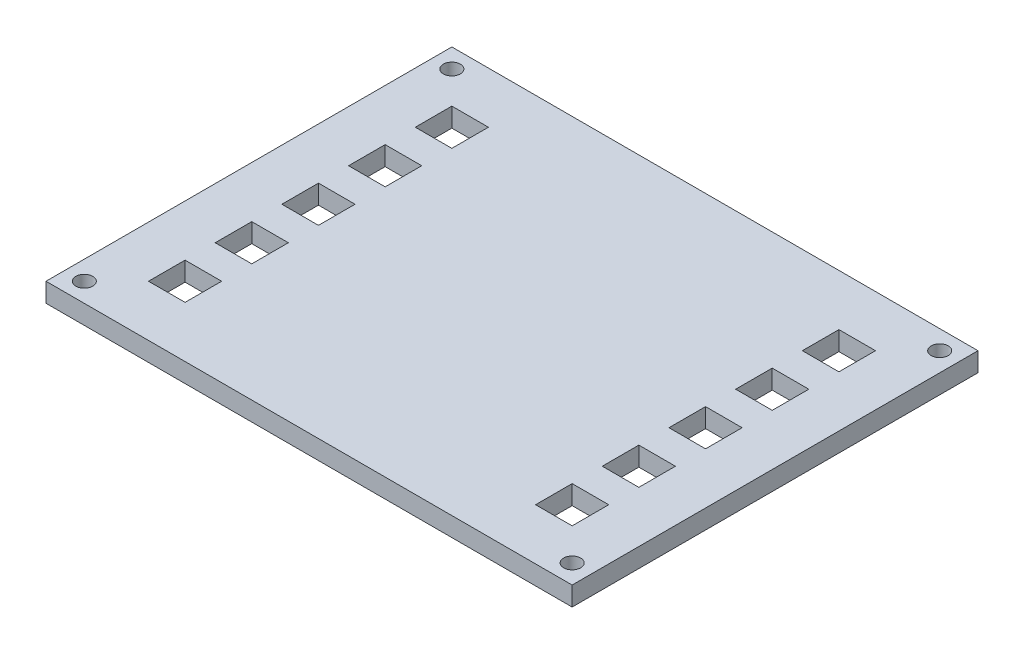
SolidWorks part; units mm, degrees
material "Maple"
ref_plane "Front Plane" through (0, 0, 0) normal (0, 0, 1) x (1, 0, 0)
ref_plane "Top Plane" through (0, 0, 0) normal (0, 1, 0) x (1, 0, 0)
ref_plane "Right Plane" through (0, 0, 0) normal (1, 0, 0) x (0, 0, -1)
sketch "Sketch1" plane through (0, 0, 0) normal (0, 1, 0) x (1, 0, 0)
  line L1 (-50.085, 40.085) -> (50.085, 40.085)
  line L2 (-50.085, 40.085) -> (-50.085, -40.085)
  line L3 (-50.085, -40.085) -> (50.085, -40.085)
  line L4 (50.085, 40.085) -> (50.085, -40.085)
  line L5 (-50.085, 40.085) -> (50.085, -40.085) construction
  line L6 (-50.085, -40.085) -> (50.085, 40.085) construction
  point P0 (0, 0)
  dimension "D1" = 100.17
  dimension "D2" = 80.17
extrude "Boss-Extrude1" add sketch "Sketch1" along normal blind 3.175
sketch "Sketch2" plane through (0, 3.175, 0) normal (0, 1, 0) x (1, 0, 0)
  line L0 (-35.3, 25.3) -> (35.3, 25.3) construction
  line L1 (-37.3, 27.3) -> (37.3, 27.3) construction
  line L2 (-37.3, 27.3) -> (-37.3, -27.3) construction
  line L3 (-37.3, -27.3) -> (37.3, -27.3) construction
  line L4 (37.3, 27.3) -> (37.3, -27.3) construction
  line L5 (-37.3, 27.3) -> (37.3, -27.3) construction
  line L6 (-37.3, -27.3) -> (37.3, 27.3) construction
  line L7 (35.3, 25.3) -> (35.3, -25.3) construction
  line L8 (-35.3, -25.3) -> (35.3, -25.3) construction
  line L9 (-35.3, 25.3) -> (-35.3, -25.3) construction
  line L10 (35.3, 19.05) -> (29.05, 19.05) construction
  line L19 (0, 0) -> (0, 10.7389) construction
  line L24 (-35.3, 25.3) -> (-29.05, 25.3) construction
  line L25 (-35.3, 25.3) -> (-35.3, 19.05) construction
  line L30 (-35.3, 19.05) -> (-29.05, 19.05) construction
  line L31 (-29.05, 25.3) -> (-29.05, 19.05) construction
  line L36 (29.05, 25.3) -> (29.05, 19.05) construction
  line L37 (35.3, 25.3) -> (29.05, 25.3) construction
  line L58 (35.3, 25.3) -> (35.3, 19.05) construction
  line L59 (-35.215, 25.215) -> (-29.135, 25.215)
  line L60 (-29.135, 25.215) -> (-29.135, 19.135)
  line L61 (-35.215, 19.135) -> (-29.135, 19.135)
  line L62 (-35.215, 25.215) -> (-35.215, 19.135)
  line L63 (35.215, 19.135) -> (29.135, 19.135)
  line L64 (29.135, 25.215) -> (29.135, 19.135)
  line L65 (35.215, 25.215) -> (29.135, 25.215)
  line L66 (35.215, 25.215) -> (35.215, 19.135)
  line L67 (-35.3, -25.215) -> (35.3, -25.215) construction
  point P0 (0, 0)
  dimension "D1" = 74.6
  dimension "D2" = 54.6
  dimension "D4" = 6.25
  dimension "D5" = 6.25
  dimension "D3" = 2
  dimension "D6" = 0.085
  dimension "D7" = 0.085
  dimension "D8" = 0.085
extrude "Cut-Extrude2" cut sketch "Sketch2" against normal through all
pattern_linear "LPattern1" count 5 spacing 11.0875 along (0, 0, 1) of "Cut-Extrude2"
sketch "Sketch5" plane through (0, 3.175, 0) normal (0, 1, 0) x (1, 0, 0)
  line L0 (-53.735, 43.735) -> (-53.735, -43.735)
  line L1 (-43.735, 33.735) -> (43.735, 33.735)
  line L2 (-43.735, 33.735) -> (-43.735, -33.735)
  line L3 (-43.735, -33.735) -> (43.735, -33.735)
  line L4 (43.735, 33.735) -> (43.735, -33.735)
  line L5 (-43.735, 33.735) -> (43.735, -33.735) construction
  line L6 (-43.735, -33.735) -> (43.735, 33.735) construction
  line L7 (-53.735, -43.735) -> (53.735, -43.735)
  line L8 (53.735, 43.735) -> (53.735, -43.735)
  line L9 (-53.735, 43.735) -> (53.735, 43.735)
  point P0 (0, 0)
  dimension "D1" = 87.47
  dimension "D2" = 67.47
  dimension "D3" = 10
extrude "Cut-Extrude4" cut sketch "Sketch5" against normal blind 10
sketch "Sketch6" plane through (0, 3.175, 0) normal (0, 1, 0) x (1, 0, 0)
  line L0 (-43.735, 33.735) -> (-40.553, 30.553) construction
  line L1 (43.735, 33.735) -> (-43.735, 33.735) construction
  line L2 (0, 0) -> (0, -4.5663) construction
  line L3 (0, 0) -> (-6.9536, 0) construction
  circle A0 centre (-40.553, 30.553) radius 1.415
  circle A1 centre (-40.553, -30.553) radius 1.415
  circle A2 centre (40.553, -30.553) radius 1.415
  circle A3 centre (40.553, 30.553) radius 1.415
  dimension "D3" = 2.83
  dimension "D1" = 45
  dimension "D2" = 4.5
extrude "Cut-Extrude5" cut sketch "Sketch6" against normal blind 10
equation "\"length\"=100"
equation "\"D1@Sketch1\"=\"length\" + 2*\"kerf\""
equation "\"width\"=80"
equation "\"D2@Sketch1\"=\"width\" + 2*\"kerf\""
equation "\"depth\"= 6.35"
equation "\"new\"= 3.175"
equation "\"D1@Boss-Extrude1\"=\"new\""
equation "\"D1@Sketch2\"=\"length\" - 4*\"depth\""
equation "\"D2@Sketch2\"=\"width\" - 4*\"depth\""
equation "\"cut\"= 6.25"
equation "\"D4@Sketch2\"=\"cut\""
equation "\"D5@Sketch2\"=\"cut\""
equation "\"kerf\"= 0.17 / 2"
equation "\"D1@Sketch5\"=87.3 + 2*\"kerf\""
equation "\"D2@Sketch5\"=67.3 + 2*\"kerf\""
equation "\"D3@Sketch6\"= 3 - 2*\"kerf\""
